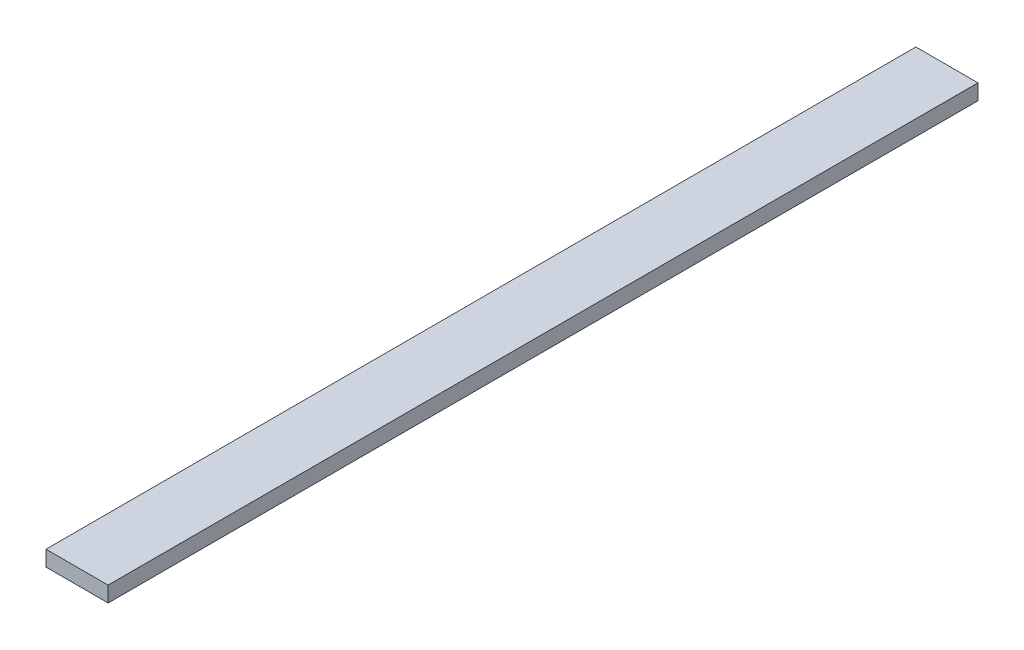
SolidWorks part; units mm, degrees
ref_plane "Front Plane" through (0, 0, 0) normal (0, 0, 1) x (1, 0, 0)
ref_plane "Top Plane" through (0, 0, 0) normal (0, 1, 0) x (1, 0, 0)
ref_plane "Right Plane" through (0, 0, 0) normal (1, 0, 0) x (0, 0, -1)
sketch "Sketch1" plane through (0, 0, 0) normal (0, 1, 0) x (1, 0, 0)
  line L1 (0, 0) -> (25.4, 0)
  line L2 (0, 0) -> (0, 355.6)
  line L3 (0, 355.6) -> (25.4, 355.6)
  line L4 (25.4, 0) -> (25.4, 355.6)
  dimension "D1" = 25.4
  dimension "D2" = 355.6
extrude "Boss-Extrude1" add sketch "Sketch1" along normal blind 6.35
